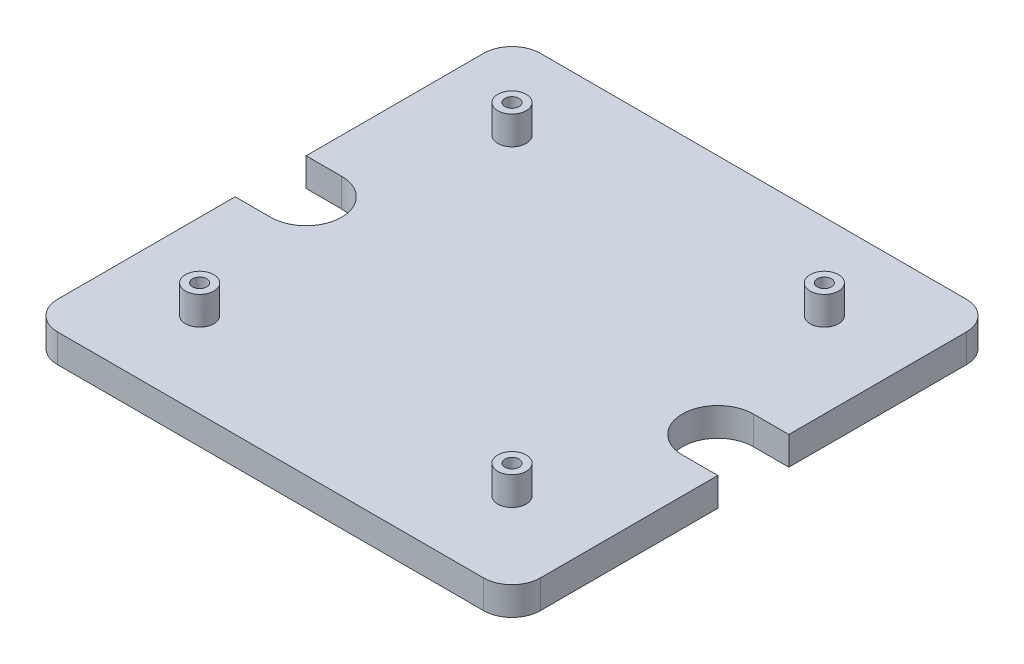
SolidWorks part; units mm, degrees
ref_plane "Front Plane" through (0, 0, 0) normal (0, 0, 1) x (1, 0, 0)
ref_plane "Top Plane" through (0, 0, 0) normal (0, 1, 0) x (1, 0, 0)
ref_plane "Right Plane" through (0, 0, 0) normal (1, 0, 0) x (0, 0, -1)
sketch "Sketch1" plane through (0, 0, 0) normal (0, 1, 0) x (1, 0, 0)
  line L0 (25, 25) -> (145, 25)
  line L1 (0, 0) -> (170, 0)
  line L2 (0, 0) -> (0, 170)
  line L3 (0, 170) -> (170, 170)
  line L4 (170, 0) -> (170, 170)
  line L5 (145, 25) -> (145, 145)
  line L6 (25, 145) -> (145, 145)
  line L7 (25, 25) -> (25, 145)
  line L8 (25, 25) -> (30, 25)
  circle A0 centre (30, 30) radius 5
  circle A1 centre (30, 30) radius 2.5
  circle A2 centre (140, 30) radius 5
  circle A3 centre (140, 30) radius 2.5
  circle A4 centre (30, 140) radius 5
  circle A5 centre (30, 140) radius 2.5
  circle A6 centre (140, 140) radius 2.5
  circle A7 centre (140, 140) radius 5
  dimension "D4" = 2
  dimension "D1" = 170
  dimension "D2" = 170
  dimension "D3" = 25
  dimension "D5" = 2
sketch "Sketch2" plane through (0, 0, 0) normal (0, 1, 0) x (1, 0, 0)
  line L1 (0, 0) -> (170, 0)
  line L2 (0, 0) -> (0, 170)
  line L3 (0, 170) -> (170, 170)
  line L4 (170, 0) -> (170, 170)
extrude "Boss-Extrude1" add sketch "Sketch2" along normal blind 10
extrude "Boss-Extrude2" add sketch "Sketch1" along normal blind 20 contours A4 A5 | A0 A1 | A2 A3 | A6 | A7 A6
fillet "Fillet1" radius 10 4 edges at (170, 5, 0) (170, 5, -170) (0, 5, -170) (0, 5, 0)
sketch "Sketch3" plane through (0, 0, 0) normal (0, -1, 0) x (-1, 0, 0)
  line L0 (-15.5367, 35) -> (-129.2621, 35)
  line L1 (-10, 0) -> (-160, 0) construction
  line L2 (-41.0491, 135) -> (-107.9424, 135)
  line L3 (-160, 170) -> (-10, 170) construction
  line L4 (-30.625, -36.8564) -> (-30.625, 185.8966)
  line L5 (0, 160) -> (0, 10) construction
  line L6 (-139.375, -36.8409) -> (-139.375, 111.8915)
  line L7 (-170, 10) -> (-170, 160) construction
  circle A0 centre (-30.625, 135) radius 5
  circle A1 centre (-139.375, 135) radius 5
  circle A2 centre (-139.375, 35) radius 5
  circle A3 centre (-30.625, 35) radius 5
  dimension "D5" = 2
  dimension "D1" = 35
  dimension "D2" = 35
  dimension "D3" = 30.625
  dimension "D4" = 30.625
  dimension "D6" = 2
extrude "Cut-Extrude1" cut sketch "Sketch3" against normal blind 6.5
sketch "Sketch4" plane through (0, 10, 0) normal (0, 1, 0) x (1, 0, 0)
  line L0 (2.9289, 167.0711) -> (167.0711, 2.9289)
  line L1 (85, 85) -> (25, 85)
  line L2 (12.5, 97.5) -> (0, 97.5)
  line L3 (0, 160) -> (0, 10) construction
  line L4 (12.5, 72.5) -> (0, 72.5)
  line L5 (85, 85) -> (85, 57.8592) construction
  line L6 (157.5, 72.5) -> (170, 72.5)
  line L7 (157.5, 97.5) -> (170, 97.5)
  line L8 (0, 97.5) -> (0, 72.5)
  line L9 (170, 97.5) -> (170, 72.5)
  arc A0 (10, 170) -> (0, 160) centre (10, 160) ccw construction
  arc A1 (160, 0) -> (170, 10) centre (160, 10) ccw construction
  arc A2 (12.5, 72.5) -> (12.5, 97.5) centre (12.5, 85) ccw
  arc A3 (157.5, 72.5) -> (157.5, 97.5) centre (157.5, 85) cw
  line M11 (170, 10) -> (170, 160)
  line M15 (0, 160) -> (0, 10)
extrude "Cut-Extrude2" cut sketch "Sketch4" against normal through all contours L4 A2 L2 M15 | A3 L6 L7 M11
